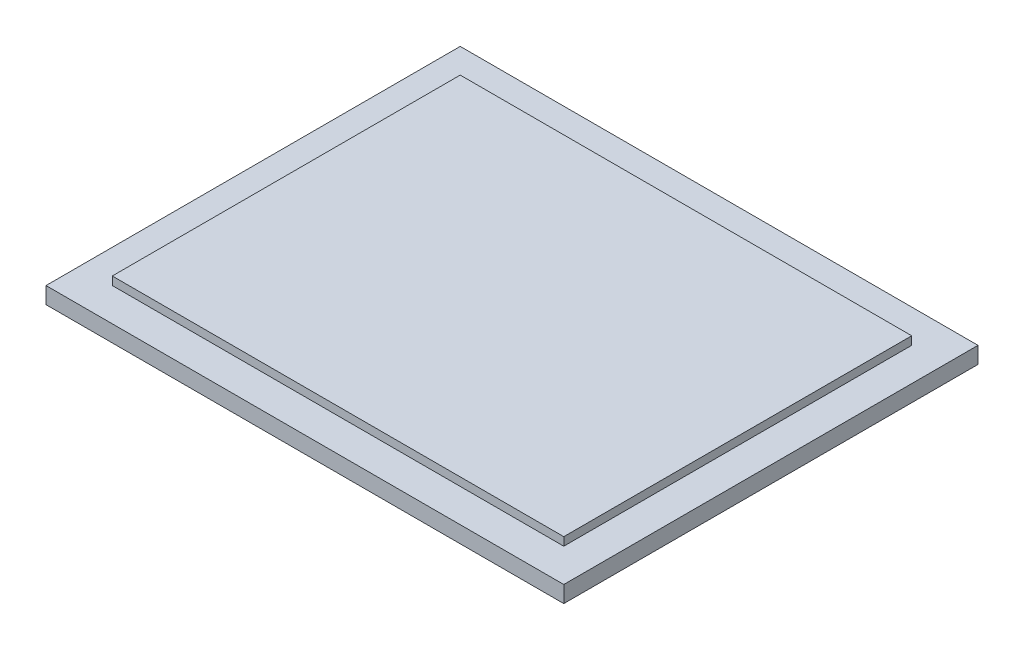
SolidWorks part; units mm, degrees
ref_plane "Front Plane" through (0, 0, 0) normal (0, 0, 1) x (1, 0, 0)
ref_plane "Top Plane" through (0, 0, 0) normal (0, 1, 0) x (1, 0, 0)
ref_plane "Right Plane" through (0, 0, 0) normal (1, 0, 0) x (0, 0, -1)
sketch "Sketch1" plane through (0, 0, 0) normal (0, 1, 0) x (1, 0, 0)
  line L1 (-53.9957, 19.2062) -> (71.0043, 19.2062)
  line L2 (-53.9957, 19.2062) -> (-53.9957, -80.7938)
  line L3 (-53.9957, -80.7938) -> (71.0043, -80.7938)
  line L4 (71.0043, 19.2062) -> (71.0043, -80.7938)
  dimension "D1" = 125
  dimension "D2" = 100
extrude "Boss-Extrude1" add sketch "Sketch1" along normal blind 4
sketch "Sketch2" plane through (0, 4, 0) normal (0, 1, 0) x (1, 0, 0)
  line L0 (71.0043, 19.2062) -> (-53.9957, 19.2062) construction
  line L1 (-45.9957, -72.7938) -> (63.0043, -72.7938)
  line L2 (-45.9957, -72.7938) -> (-45.9957, 11.2062)
  line L3 (-45.9957, 11.2062) -> (63.0043, 11.2062)
  line L4 (63.0043, -72.7938) -> (63.0043, 11.2062)
  line L5 (71.0043, -80.7938) -> (71.0043, 19.2062) construction
  point P4 (8.5043, 11.2062)
  point P5 (8.5043, 19.2062)
  point P6 (63.0043, -30.7938)
  point P9 (71.0043, -30.7938)
  dimension "D1" = 109
  dimension "D2" = 84
extrude "Boss-Extrude2" add sketch "Sketch2" along normal blind 2
